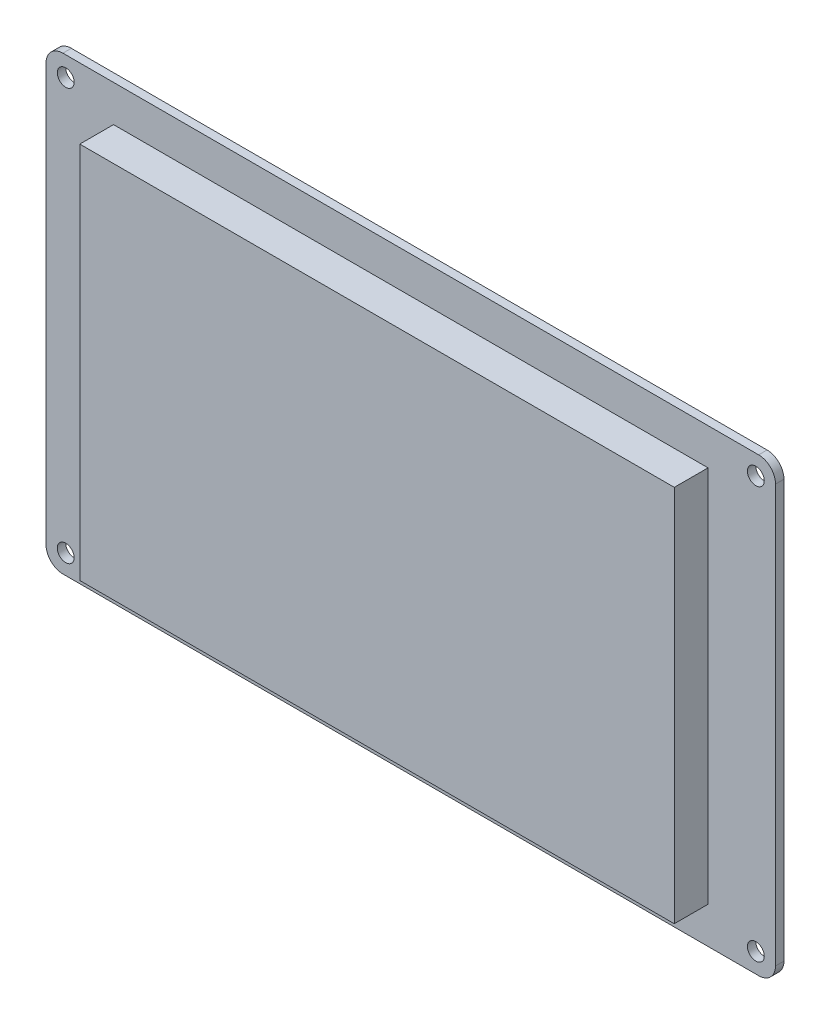
SolidWorks part; units mm, degrees
ref_plane "Front Plane" through (0, 0, 0) normal (0, 0, 1) x (1, 0, 0)
ref_plane "Top Plane" through (0, 0, 0) normal (0, 1, 0) x (1, 0, 0)
ref_plane "Right Plane" through (0, 0, 0) normal (1, 0, 0) x (0, 0, -1)
sketch "Sketch1" plane through (0, 0, 0) normal (0, 0, 1) x (1, 0, 0)
  line L1 (-52.85, 33.6) -> (52.85, 33.6)
  line L2 (-52.85, 33.6) -> (-52.85, -33.6)
  line L3 (-52.85, -33.6) -> (52.85, -33.6)
  line L4 (52.85, 33.6) -> (52.85, -33.6)
  dimension "D1" = 67.2
  dimension "D2" = 33.6
  dimension "D3" = 105.7
  dimension "D4" = 52.85
extrude "Boss-Extrude1" add sketch "Sketch1" along normal blind 6
sketch "Sketch2" plane through (0, 0, 0) normal (0, 0, -1) x (-1, 0, 0)
  line L1 (-64.85, -40.1) -> (64.85, -40.1)
  line L2 (-64.85, -40.1) -> (-64.85, 40.1)
  line L3 (-64.85, 40.1) -> (64.85, 40.1)
  line L4 (64.85, -40.1) -> (64.85, 40.1)
  line L5 (-64.85, -40.1) -> (64.85, 40.1) construction
  line L6 (-64.85, 40.1) -> (64.85, -40.1) construction
  line L7 (52.85, -33.6) -> (-52.85, -33.6) construction
  line L8 (52.85, 33.6) -> (52.85, -33.6) construction
  point P0 (0, 0)
  dimension "D1" = 12
  dimension "D2" = 6.5
extrude "Boss-Extrude2" add sketch "Sketch2" along normal blind 1.5
sketch "Sketch3" plane through (0, 0, 0) normal (0, 0, 1) x (1, 0, 0)
  line L0 (-64.85, 40.1) -> (64.85, 40.1) construction
  line L1 (64.85, 40.1) -> (64.85, -40.1) construction
  line L2 (64.85, -40.1) -> (-64.85, -40.1) construction
  line L3 (0, 0) -> (0, -28.0891) construction
  circle A0 centre (61.35, 36.6) radius 1.5
  circle A1 centre (61.35, -36.6) radius 1.5
  circle A4 centre (-61.35, -36.6) radius 1.5
  circle A5 centre (-61.35, 36.6) radius 1.5
  dimension "D3" = 3
  dimension "D6" = 3
  dimension "D1" = 3.5
  dimension "D2" = 3.5
  dimension "D7" = 3.5
  dimension "D8" = 3.5
extrude "Cut-Extrude1" cut sketch "Sketch3" against normal blind 1.5
fillet "Fillet1" radius 3 4 edges at (64.85, -40.1, -0.75) (-64.85, -40.1, -0.75) (-64.85, 40.1, -0.75) (64.85, 40.1, -0.75)
